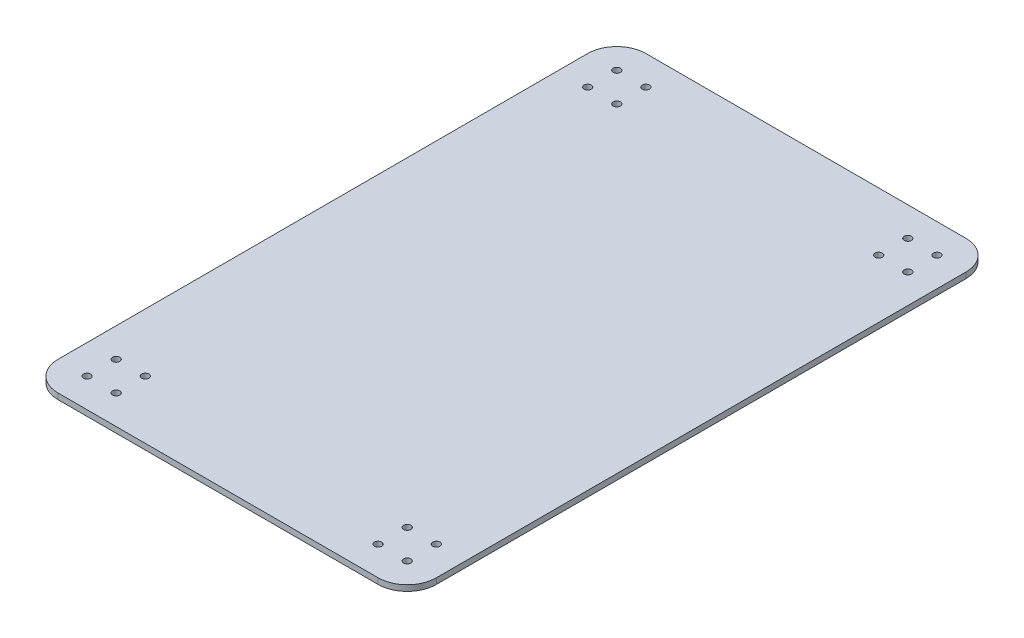
SolidWorks part; units mm, degrees
ref_plane "Front Plane" through (0, 0, 0) normal (0, 0, 1) x (1, 0, 0)
ref_plane "Top Plane" through (0, 0, 0) normal (0, 1, 0) x (1, 0, 0)
ref_plane "Right Plane" through (0, 0, 0) normal (1, 0, 0) x (0, 0, -1)
sketch "Sketch1" plane through (0, 0, 0) normal (0, 1, 0) x (1, 0, 0)
  line L1 (-147.2601, 231.3371) -> (132.1399, 231.3371)
  line L2 (-172.6601, 205.9371) -> (-172.6601, -256.3429)
  line L3 (-147.2601, -281.7429) -> (132.1399, -281.7429)
  line L4 (157.5399, 205.9371) -> (157.5399, -256.3429)
  circle A0 centre (-147.2601, 205.9371) radius 3.175
  circle A1 centre (-121.8601, 205.9371) radius 3.175
  circle A2 centre (-121.8601, 180.5371) radius 3.175
  circle A3 centre (-147.2601, 180.5371) radius 3.175
  circle A4 centre (132.1399, 180.5371) radius 3.175
  circle A5 centre (106.7399, 180.5371) radius 3.175
  circle A6 centre (106.7399, 205.9371) radius 3.175
  circle A7 centre (132.1399, 205.9371) radius 3.175
  circle A8 centre (132.1399, -256.3429) radius 3.175
  circle A9 centre (106.7399, -256.3429) radius 3.175
  circle A10 centre (106.7399, -230.9429) radius 3.175
  circle A11 centre (132.1399, -230.9429) radius 3.175
  circle A12 centre (-121.8601, -256.3429) radius 3.175
  circle A13 centre (-147.2601, -256.3429) radius 3.175
  circle A14 centre (-147.2601, -230.9429) radius 3.175
  circle A15 centre (-121.8601, -230.9429) radius 3.175
  arc A16 (-172.6601, -256.3429) -> (-147.2601, -281.7429) centre (-147.2601, -256.3429) ccw
  arc A17 (132.1399, -281.7429) -> (157.5399, -256.3429) centre (132.1399, -256.3429) ccw
  arc A18 (132.1399, 231.3371) -> (157.5399, 205.9371) centre (132.1399, 205.9371) cw
  arc A19 (-147.2601, 231.3371) -> (-172.6601, 205.9371) centre (-147.2601, 205.9371) ccw
  point P38 (-172.6601, -281.7429)
  point P43 (157.5399, 231.3371)
  point P46 (-172.6601, 231.3371)
  dimension "D3" = 25.4
  dimension "D5" = 6.35
  dimension "D10" = 25.4
  dimension "D12" = 25.4
  dimension "D1" = 513.08
  dimension "D2" = 330.2
  dimension "D4" = 25.4
  dimension "D11" = 25.4
  dimension "D6" = 2
  dimension "D7" = 2
  dimension "D8" = 2
  dimension "D9" = 2
extrude "Boss-Extrude1" add sketch "Sketch1" along normal blind 5.08
